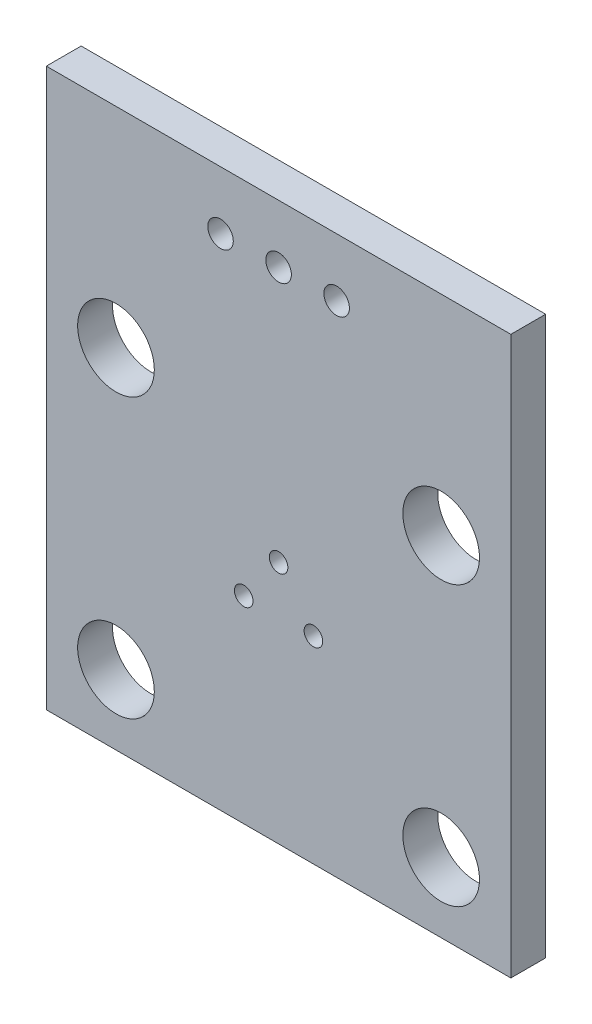
SolidWorks part; units mm, degrees
ref_plane "Спереди" through (0, 0, 0) normal (0, 0, 1) x (1, 0, 0)
ref_plane "Сверху" through (0, 0, 0) normal (0, 1, 0) x (1, 0, 0)
ref_plane "Справа" through (0, 0, 0) normal (1, 0, 0) x (0, 0, -1)
sketch "Эскиз1" plane through (0, 0, 0) normal (0, 0, 1) x (1, 0, 0)
  line L1 (0, 0) -> (20, 0)
  line L2 (0, 0) -> (0, 24)
  line L3 (0, 24) -> (20, 24)
  line L4 (20, 0) -> (20, 24)
  circle A0 centre (3, 3) radius 1.65
  circle A1 centre (17, 3) radius 1.65
  circle A2 centre (17, 15) radius 1.65
  circle A3 centre (3, 15) radius 1.65
  circle A4 centre (7.5, 21.5) radius 0.55
  circle A5 centre (10, 21.5) radius 0.55
  circle A6 centre (12.5, 21.5) radius 0.55
  circle A7 centre (10, 10.5) radius 0.4
  circle A8 centre (11.5, 8.5) radius 0.4
  circle A9 centre (8.5, 8.5) radius 0.4
  dimension "D3" = 14
  dimension "D4" = 3
  dimension "D5" = 3
  dimension "D6" = 12
  dimension "D7" = 3.3
  dimension "D8" = 1.1
  dimension "D9" = 2.5
  dimension "D10" = 2.5
  dimension "D11" = 10
  dimension "D13" = 10.5
  dimension "D14" = 2
  dimension "D15" = 0.8
  dimension "D16" = 1.5
  dimension "D17" = 1.5
  dimension "D1" = 20
  dimension "D2" = 24
  dimension "D12" = 2.5
extrude "Бобышка-Вытянуть1" add sketch "Эскиз1" along normal blind 1.5
